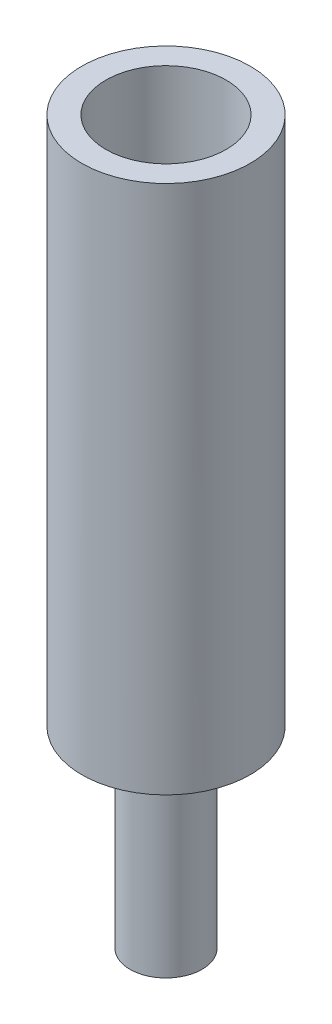
SolidWorks part; units mm, degrees
ref_plane "Front Plane" through (0, 0, 0) normal (0, 0, 1) x (1, 0, 0)
ref_plane "Top Plane" through (0, 0, 0) normal (0, 1, 0) x (1, 0, 0)
ref_plane "Right Plane" through (0, 0, 0) normal (1, 0, 0) x (0, 0, -1)
sketch "Sketch1" plane through (0, 0, 0) normal (0, 1, 0) x (1, 0, 0)
  circle A0 centre (0, 0) radius 3.5
  dimension "D1" = 7
extrude "Boss-Extrude1" add sketch "Sketch1" along normal blind 30
sketch "Sketch2" plane through (0, 30, 0) normal (0, 1, 0) x (1, 0, 0)
  circle A0 centre (0, 0) radius 2.5
extrude "Cut-Extrude1" cut sketch "Sketch2" against normal blind 20
sketch "Sketch3" plane through (0, 0, 0) normal (0, -1, 0) x (1, 0, 0)
  circle A0 centre (0, 0) radius 1.5
  circle A1 centre (0, 0) radius 3.5
extrude "Cut-Extrude4" cut sketch "Sketch3" against normal blind 8 contours A0 | A1
